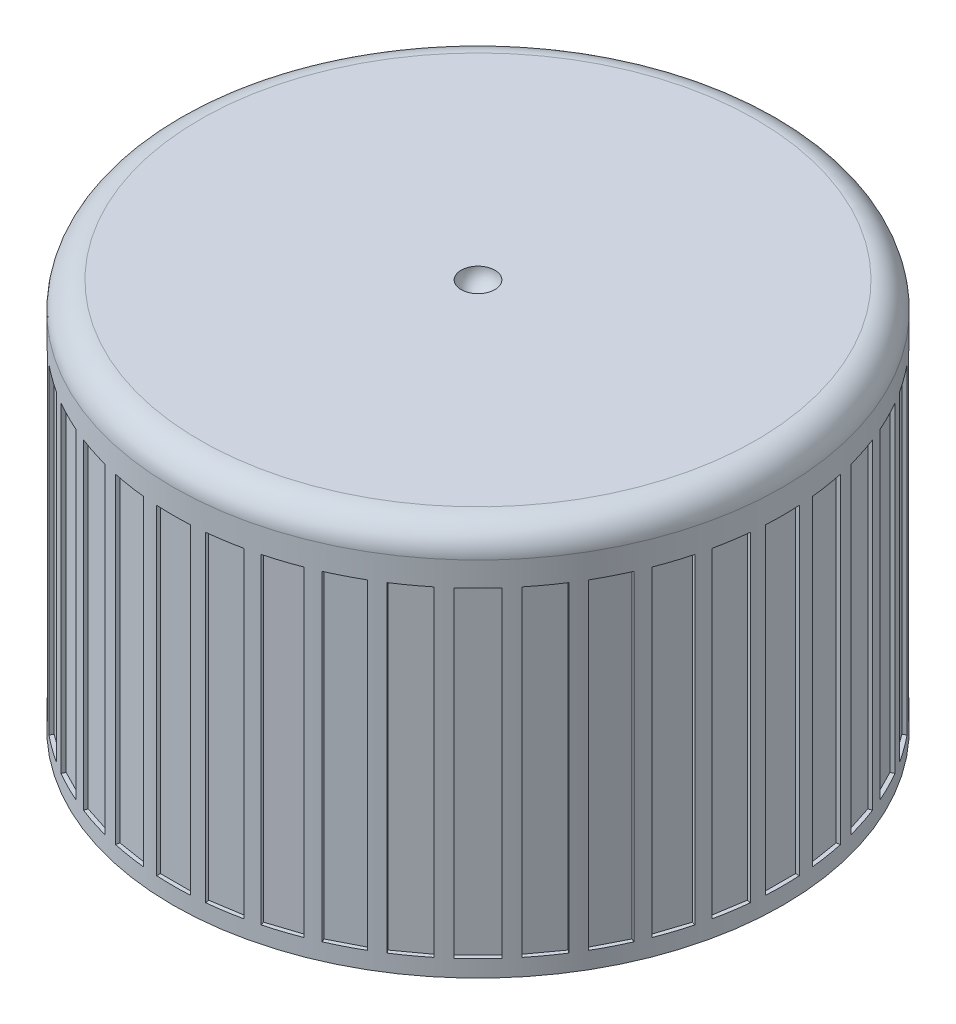
SolidWorks part; units mm, degrees
ref_plane "Front Plane" through (0, 0, 0) normal (0, 0, 1) x (1, 0, 0)
ref_plane "Top Plane" through (0, 0, 0) normal (0, 1, 0) x (1, 0, 0)
ref_plane "Right Plane" through (0, 0, 0) normal (1, 0, 0) x (0, 0, -1)
sketch "Sketch1" plane through (0, 0, 0) normal (0, 0, 1) x (1, 0, 0)
  line L0 (0, 0) -> (9.03, 0) construction
  line L1 (0, 0) -> (0, 7.53) construction
  line L2 (8.23, 11.52) -> (0.5, 11.52)
  line L3 (9.03, 10.72) -> (9.03, 0)
  line L4 (0, 11.02) -> (0, 7.53)
  line L5 (5.51, 7.53) -> (4.3, 7.53)
  line L6 (5.51, 7.53) -> (5.51, 10.02)
  line L7 (5.51, 10.02) -> (6.73, 10.02)
  line L9 (8.5692, 0) -> (9.03, 0)
  line L10 (7.53, 2.04) -> (7.53, 9.22)
  line L16 (3.5, 7.53) -> (2, 7.53)
  line L17 (7.53, 1.52) -> (7.53, 2.04) construction
  line L18 (0, 7.23) -> (0, 7.53)
  line L19 (2, 7.53) -> (2, 7.23)
  line L20 (7.53, 1) -> (7.53, 0) construction
  line L21 (3.9, 7.53) -> (4.3, 7.53) construction
  line L22 (7.53, 0) -> (8.5692, 0) construction
  line L23 (3.9, 7.53) -> (3.5, 7.53) construction
  line L24 (0, 11.52) -> (0, 11.02) construction
  line L25 (0, 11.52) -> (0.5, 11.52) construction
  line L26 (2, 7.23) -> (0, 7.23)
  line L28 (7.53, 1) -> (7.9086, 1.3786)
  line L29 (7.9086, 1.6614) -> (7.53, 2.04)
  line L30 (7.53, 2.04) -> (7.53, 1.52) construction
  line L31 (7.53, 1.52) -> (7.53, 1) construction
  arc A1 (3.5, 7.53) -> (4.3, 7.53) centre (3.9, 7.53) cw
  arc A5 (9.03, 10.72) -> (8.23, 11.52) centre (8.23, 10.72) ccw
  arc A6 (7.53, 9.22) -> (6.73, 10.02) centre (6.73, 9.22) ccw
  arc A8 (0.5, 11.52) -> (0, 11.02) centre (0, 11.52) cw
  arc A9 (7.9086, 1.3786) -> (7.9086, 1.6614) centre (7.7672, 1.52) ccw
  arc A10 (8.5692, 0) -> (7.53, 1) centre (8.5692, 1.04) cw
  point P24 (8.05, 1.52)
  point P26 (7.53, 0)
  point P32 (9.03, 11.52)
  point P35 (7.53, 10.02)
  dimension "D2" = 45
  dimension "D6" = 0.4
  dimension "D15" = 1.04
  dimension "D16" = 1.04
  dimension "D19" = 0.8
  dimension "D7" = 3.9
  dimension "D9" = 0.5
  dimension "D14" = 0.2
  dimension "D1" = 1.5
  dimension "D3" = 10.02
  dimension "D4" = 1
  dimension "D5" = 1.5
  dimension "D8" = 2.02
  dimension "D10" = 2
  dimension "D11" = 2.49
  dimension "D12" = 0.3
  dimension "D13" = 45
  dimension "D17" = 0.8
  dimension "7.52" = 7.53
revolve "Revolve1" add sketch "Sketch1" angle 360 about L1
sketch "Sketch2" plane through (0, 0, 0) normal (0, -1, 0) x (1, 0, 0)
  line L0 (0, 0) -> (9.03, 0) construction
  line L1 (8.8736, -0.8992) -> (9.1205, -0.9383)
  line L2 (8.905, 0.5) -> (9.155, 0.5)
  line L3 (8.905, 0.5) -> (8.905, -0.5)
  line L4 (8.905, -0.5) -> (9.155, -0.5)
  line L5 (9.155, 0.5) -> (9.155, -0.5)
  line L6 (8.905, 0.5) -> (9.155, -0.5) construction
  line L7 (8.905, -0.5) -> (9.155, 0.5) construction
  line L8 (8.8736, -0.8992) -> (8.7171, -1.8869)
  line L9 (8.7171, -1.8869) -> (8.9641, -1.926)
  line L10 (8.7171, -1.8869) -> (9.1205, -0.9383) construction
  line L11 (9.1205, -0.9383) -> (8.9641, -1.926)
  line L12 (8.8736, -0.8992) -> (8.9641, -1.926) construction
  line L13 (8.6237, -2.2763) -> (8.8614, -2.3535)
  line L14 (8.6237, -2.2763) -> (8.3146, -3.2273)
  line L15 (8.3146, -3.2273) -> (8.5524, -3.3046)
  line L16 (8.3146, -3.2273) -> (8.8614, -2.3535) construction
  line L17 (8.8614, -2.3535) -> (8.5524, -3.3046)
  line L18 (8.6237, -2.2763) -> (8.5524, -3.3046) construction
  line L19 (8.1614, -3.5973) -> (8.3842, -3.7108)
  line L20 (8.1614, -3.5973) -> (7.7074, -4.4883)
  line L21 (7.7074, -4.4883) -> (7.9302, -4.6018)
  line L22 (7.7074, -4.4883) -> (8.3842, -3.7108) construction
  line L23 (8.3842, -3.7108) -> (7.9302, -4.6018)
  line L24 (8.1614, -3.5973) -> (7.9302, -4.6018) construction
  line L25 (7.4982, -4.8297) -> (7.7004, -4.9767)
  line L26 (7.4982, -4.8297) -> (6.9104, -5.6387)
  line L27 (6.9104, -5.6387) -> (7.1127, -5.7857)
  line L28 (6.9104, -5.6387) -> (7.7004, -4.9767) construction
  line L29 (7.7004, -4.9767) -> (7.1127, -5.7857)
  line L30 (7.4982, -4.8297) -> (7.1127, -5.7857) construction
  line L31 (6.6503, -5.9432) -> (6.8271, -6.12)
  line L32 (6.6503, -5.9432) -> (5.9432, -6.6503)
  line L33 (5.9432, -6.6503) -> (6.12, -6.8271)
  line L34 (5.9432, -6.6503) -> (6.8271, -6.12) construction
  line L35 (6.8271, -6.12) -> (6.12, -6.8271)
  line L36 (6.6503, -5.9432) -> (6.12, -6.8271) construction
  line L37 (5.6387, -6.9104) -> (5.7857, -7.1127)
  line L38 (5.6387, -6.9104) -> (4.8297, -7.4982)
  line L39 (4.8297, -7.4982) -> (4.9767, -7.7004)
  line L40 (4.8297, -7.4982) -> (5.7857, -7.1127) construction
  line L41 (5.7857, -7.1127) -> (4.9767, -7.7004)
  line L42 (5.6387, -6.9104) -> (4.9767, -7.7004) construction
  line L43 (4.4883, -7.7074) -> (4.6018, -7.9302)
  line L44 (4.4883, -7.7074) -> (3.5973, -8.1614)
  line L45 (3.5973, -8.1614) -> (3.7108, -8.3842)
  line L46 (3.5973, -8.1614) -> (4.6018, -7.9302) construction
  line L47 (4.6018, -7.9302) -> (3.7108, -8.3842)
  line L48 (4.4883, -7.7074) -> (3.7108, -8.3842) construction
  line L49 (3.2273, -8.3146) -> (3.3046, -8.5524)
  line L50 (3.2273, -8.3146) -> (2.2763, -8.6237)
  line L51 (2.2763, -8.6237) -> (2.3535, -8.8614)
  line L52 (2.2763, -8.6237) -> (3.3046, -8.5524) construction
  line L53 (3.3046, -8.5524) -> (2.3535, -8.8614)
  line L54 (3.2273, -8.3146) -> (2.3535, -8.8614) construction
  line L55 (1.8869, -8.7171) -> (1.926, -8.9641)
  line L56 (1.8869, -8.7171) -> (0.8992, -8.8736)
  line L57 (0.8992, -8.8736) -> (0.9383, -9.1205)
  line L58 (0.8992, -8.8736) -> (1.926, -8.9641) construction
  line L59 (1.926, -8.9641) -> (0.9383, -9.1205)
  line L60 (1.8869, -8.7171) -> (0.9383, -9.1205) construction
  line L61 (0.5, -8.905) -> (0.5, -9.155)
  line L62 (0.5, -8.905) -> (-0.5, -8.905)
  line L63 (-0.5, -8.905) -> (-0.5, -9.155)
  line L64 (-0.5, -8.905) -> (0.5, -9.155) construction
  line L65 (0.5, -9.155) -> (-0.5, -9.155)
  line L66 (0.5, -8.905) -> (-0.5, -9.155) construction
  line L67 (-0.8992, -8.8736) -> (-0.9383, -9.1205)
  line L68 (-0.8992, -8.8736) -> (-1.8869, -8.7171)
  line L69 (-1.8869, -8.7171) -> (-1.926, -8.9641)
  line L70 (-1.8869, -8.7171) -> (-0.9383, -9.1205) construction
  line L71 (-0.9383, -9.1205) -> (-1.926, -8.9641)
  line L72 (-0.8992, -8.8736) -> (-1.926, -8.9641) construction
  line L73 (-2.2763, -8.6237) -> (-2.3535, -8.8614)
  line L74 (-2.2763, -8.6237) -> (-3.2273, -8.3146)
  line L75 (-3.2273, -8.3146) -> (-3.3046, -8.5524)
  line L76 (-3.2273, -8.3146) -> (-2.3535, -8.8614) construction
  line L77 (-2.3535, -8.8614) -> (-3.3046, -8.5524)
  line L78 (-2.2763, -8.6237) -> (-3.3046, -8.5524) construction
  line L79 (-3.5973, -8.1614) -> (-3.7108, -8.3842)
  line L80 (-3.5973, -8.1614) -> (-4.4883, -7.7074)
  line L81 (-4.4883, -7.7074) -> (-4.6018, -7.9302)
  line L82 (-4.4883, -7.7074) -> (-3.7108, -8.3842) construction
  line L83 (-3.7108, -8.3842) -> (-4.6018, -7.9302)
  line L84 (-3.5973, -8.1614) -> (-4.6018, -7.9302) construction
  line L85 (-4.8297, -7.4982) -> (-4.9767, -7.7004)
  line L86 (-4.8297, -7.4982) -> (-5.6387, -6.9104)
  line L87 (-5.6387, -6.9104) -> (-5.7857, -7.1127)
  line L88 (-5.6387, -6.9104) -> (-4.9767, -7.7004) construction
  line L89 (-4.9767, -7.7004) -> (-5.7857, -7.1127)
  line L90 (-4.8297, -7.4982) -> (-5.7857, -7.1127) construction
  line L91 (-5.9432, -6.6503) -> (-6.12, -6.8271)
  line L92 (-5.9432, -6.6503) -> (-6.6503, -5.9432)
  line L93 (-6.6503, -5.9432) -> (-6.8271, -6.12)
  line L94 (-6.6503, -5.9432) -> (-6.12, -6.8271) construction
  line L95 (-6.12, -6.8271) -> (-6.8271, -6.12)
  line L96 (-5.9432, -6.6503) -> (-6.8271, -6.12) construction
  line L97 (-6.9104, -5.6387) -> (-7.1127, -5.7857)
  line L98 (-6.9104, -5.6387) -> (-7.4982, -4.8297)
  line L99 (-7.4982, -4.8297) -> (-7.7004, -4.9767)
  line L100 (-7.4982, -4.8297) -> (-7.1127, -5.7857) construction
  line L101 (-7.1127, -5.7857) -> (-7.7004, -4.9767)
  line L102 (-6.9104, -5.6387) -> (-7.7004, -4.9767) construction
  line L103 (-7.7074, -4.4883) -> (-7.9302, -4.6018)
  line L104 (-7.7074, -4.4883) -> (-8.1614, -3.5973)
  line L105 (-8.1614, -3.5973) -> (-8.3842, -3.7108)
  line L106 (-8.1614, -3.5973) -> (-7.9302, -4.6018) construction
  line L107 (-7.9302, -4.6018) -> (-8.3842, -3.7108)
  line L108 (-7.7074, -4.4883) -> (-8.3842, -3.7108) construction
  line L109 (-8.3146, -3.2273) -> (-8.5524, -3.3046)
  line L110 (-8.3146, -3.2273) -> (-8.6237, -2.2763)
  line L111 (-8.6237, -2.2763) -> (-8.8614, -2.3535)
  line L112 (-8.6237, -2.2763) -> (-8.5524, -3.3046) construction
  line L113 (-8.5524, -3.3046) -> (-8.8614, -2.3535)
  line L114 (-8.3146, -3.2273) -> (-8.8614, -2.3535) construction
  line L115 (-8.7171, -1.8869) -> (-8.9641, -1.926)
  line L116 (-8.7171, -1.8869) -> (-8.8736, -0.8992)
  line L117 (-8.8736, -0.8992) -> (-9.1205, -0.9383)
  line L118 (-8.8736, -0.8992) -> (-8.9641, -1.926) construction
  line L119 (-8.9641, -1.926) -> (-9.1205, -0.9383)
  line L120 (-8.7171, -1.8869) -> (-9.1205, -0.9383) construction
  line L121 (-8.905, -0.5) -> (-9.155, -0.5)
  line L122 (-8.905, -0.5) -> (-8.905, 0.5)
  line L123 (-8.905, 0.5) -> (-9.155, 0.5)
  line L124 (-8.905, 0.5) -> (-9.155, -0.5) construction
  line L125 (-9.155, -0.5) -> (-9.155, 0.5)
  line L126 (-8.905, -0.5) -> (-9.155, 0.5) construction
  line L127 (-8.8736, 0.8992) -> (-9.1205, 0.9383)
  line L128 (-8.8736, 0.8992) -> (-8.7171, 1.8869)
  line L129 (-8.7171, 1.8869) -> (-8.9641, 1.926)
  line L130 (-8.7171, 1.8869) -> (-9.1205, 0.9383) construction
  line L131 (-9.1205, 0.9383) -> (-8.9641, 1.926)
  line L132 (-8.8736, 0.8992) -> (-8.9641, 1.926) construction
  line L133 (-8.6237, 2.2763) -> (-8.8614, 2.3535)
  line L134 (-8.6237, 2.2763) -> (-8.3146, 3.2273)
  line L135 (-8.3146, 3.2273) -> (-8.5524, 3.3046)
  line L136 (-8.3146, 3.2273) -> (-8.8614, 2.3535) construction
  line L137 (-8.8614, 2.3535) -> (-8.5524, 3.3046)
  line L138 (-8.6237, 2.2763) -> (-8.5524, 3.3046) construction
  line L139 (-8.1614, 3.5973) -> (-8.3842, 3.7108)
  line L140 (-8.1614, 3.5973) -> (-7.7074, 4.4883)
  line L141 (-7.7074, 4.4883) -> (-7.9302, 4.6018)
  line L142 (-7.7074, 4.4883) -> (-8.3842, 3.7108) construction
  line L143 (-8.3842, 3.7108) -> (-7.9302, 4.6018)
  line L144 (-8.1614, 3.5973) -> (-7.9302, 4.6018) construction
  line L145 (-7.4982, 4.8297) -> (-7.7004, 4.9767)
  line L146 (-7.4982, 4.8297) -> (-6.9104, 5.6387)
  line L147 (-6.9104, 5.6387) -> (-7.1127, 5.7857)
  line L148 (-6.9104, 5.6387) -> (-7.7004, 4.9767) construction
  line L149 (-7.7004, 4.9767) -> (-7.1127, 5.7857)
  line L150 (-7.4982, 4.8297) -> (-7.1127, 5.7857) construction
  line L151 (-6.6503, 5.9432) -> (-6.8271, 6.12)
  line L152 (-6.6503, 5.9432) -> (-5.9432, 6.6503)
  line L153 (-5.9432, 6.6503) -> (-6.12, 6.8271)
  line L154 (-5.9432, 6.6503) -> (-6.8271, 6.12) construction
  line L155 (-6.8271, 6.12) -> (-6.12, 6.8271)
  line L156 (-6.6503, 5.9432) -> (-6.12, 6.8271) construction
  line L157 (-5.6387, 6.9104) -> (-5.7857, 7.1127)
  line L158 (-5.6387, 6.9104) -> (-4.8297, 7.4982)
  line L159 (-4.8297, 7.4982) -> (-4.9767, 7.7004)
  line L160 (-4.8297, 7.4982) -> (-5.7857, 7.1127) construction
  line L161 (-5.7857, 7.1127) -> (-4.9767, 7.7004)
  line L162 (-5.6387, 6.9104) -> (-4.9767, 7.7004) construction
  line L163 (-4.4883, 7.7074) -> (-4.6018, 7.9302)
  line L164 (-4.4883, 7.7074) -> (-3.5973, 8.1614)
  line L165 (-3.5973, 8.1614) -> (-3.7108, 8.3842)
  line L166 (-3.5973, 8.1614) -> (-4.6018, 7.9302) construction
  line L167 (-4.6018, 7.9302) -> (-3.7108, 8.3842)
  line L168 (-4.4883, 7.7074) -> (-3.7108, 8.3842) construction
  line L169 (-3.2273, 8.3146) -> (-3.3046, 8.5524)
  line L170 (-3.2273, 8.3146) -> (-2.2763, 8.6237)
  line L171 (-2.2763, 8.6237) -> (-2.3535, 8.8614)
  line L172 (-2.2763, 8.6237) -> (-3.3046, 8.5524) construction
  line L173 (-3.3046, 8.5524) -> (-2.3535, 8.8614)
  line L174 (-3.2273, 8.3146) -> (-2.3535, 8.8614) construction
  line L175 (-1.8869, 8.7171) -> (-1.926, 8.9641)
  line L176 (-1.8869, 8.7171) -> (-0.8992, 8.8736)
  line L177 (-0.8992, 8.8736) -> (-0.9383, 9.1205)
  line L178 (-0.8992, 8.8736) -> (-1.926, 8.9641) construction
  line L179 (-1.926, 8.9641) -> (-0.9383, 9.1205)
  line L180 (-1.8869, 8.7171) -> (-0.9383, 9.1205) construction
  line L181 (-0.5, 8.905) -> (-0.5, 9.155)
  line L182 (-0.5, 8.905) -> (0.5, 8.905)
  line L183 (0.5, 8.905) -> (0.5, 9.155)
  line L184 (0.5, 8.905) -> (-0.5, 9.155) construction
  line L185 (-0.5, 9.155) -> (0.5, 9.155)
  line L186 (-0.5, 8.905) -> (0.5, 9.155) construction
  line L187 (0.8992, 8.8736) -> (0.9383, 9.1205)
  line L188 (0.8992, 8.8736) -> (1.8869, 8.7171)
  line L189 (1.8869, 8.7171) -> (1.926, 8.9641)
  line L190 (1.8869, 8.7171) -> (0.9383, 9.1205) construction
  line L191 (0.9383, 9.1205) -> (1.926, 8.9641)
  line L192 (0.8992, 8.8736) -> (1.926, 8.9641) construction
  line L193 (2.2763, 8.6237) -> (2.3535, 8.8614)
  line L194 (2.2763, 8.6237) -> (3.2273, 8.3146)
  line L195 (3.2273, 8.3146) -> (3.3046, 8.5524)
  line L196 (3.2273, 8.3146) -> (2.3535, 8.8614) construction
  line L197 (2.3535, 8.8614) -> (3.3046, 8.5524)
  line L198 (2.2763, 8.6237) -> (3.3046, 8.5524) construction
  line L199 (3.5973, 8.1614) -> (3.7108, 8.3842)
  line L200 (3.5973, 8.1614) -> (4.4883, 7.7074)
  line L201 (4.4883, 7.7074) -> (4.6018, 7.9302)
  line L202 (4.4883, 7.7074) -> (3.7108, 8.3842) construction
  line L203 (3.7108, 8.3842) -> (4.6018, 7.9302)
  line L204 (3.5973, 8.1614) -> (4.6018, 7.9302) construction
  line L205 (4.8297, 7.4982) -> (4.9767, 7.7004)
  line L206 (4.8297, 7.4982) -> (5.6387, 6.9104)
  line L207 (5.6387, 6.9104) -> (5.7857, 7.1127)
  line L208 (5.6387, 6.9104) -> (4.9767, 7.7004) construction
  line L209 (4.9767, 7.7004) -> (5.7857, 7.1127)
  line L210 (4.8297, 7.4982) -> (5.7857, 7.1127) construction
  line L211 (5.9432, 6.6503) -> (6.12, 6.8271)
  line L212 (5.9432, 6.6503) -> (6.6503, 5.9432)
  line L213 (6.6503, 5.9432) -> (6.8271, 6.12)
  line L214 (6.6503, 5.9432) -> (6.12, 6.8271) construction
  line L215 (6.12, 6.8271) -> (6.8271, 6.12)
  line L216 (5.9432, 6.6503) -> (6.8271, 6.12) construction
  line L217 (6.9104, 5.6387) -> (7.1127, 5.7857)
  line L218 (6.9104, 5.6387) -> (7.4982, 4.8297)
  line L219 (7.4982, 4.8297) -> (7.7004, 4.9767)
  line L220 (7.4982, 4.8297) -> (7.1127, 5.7857) construction
  line L221 (7.1127, 5.7857) -> (7.7004, 4.9767)
  line L222 (6.9104, 5.6387) -> (7.7004, 4.9767) construction
  line L223 (7.7074, 4.4883) -> (7.9302, 4.6018)
  line L224 (7.7074, 4.4883) -> (8.1614, 3.5973)
  line L225 (8.1614, 3.5973) -> (8.3842, 3.7108)
  line L226 (8.1614, 3.5973) -> (7.9302, 4.6018) construction
  line L227 (7.9302, 4.6018) -> (8.3842, 3.7108)
  line L228 (7.7074, 4.4883) -> (8.3842, 3.7108) construction
  line L229 (8.3146, 3.2273) -> (8.5524, 3.3046)
  line L230 (8.3146, 3.2273) -> (8.6237, 2.2763)
  line L231 (8.6237, 2.2763) -> (8.8614, 2.3535)
  line L232 (8.6237, 2.2763) -> (8.5524, 3.3046) construction
  line L233 (8.5524, 3.3046) -> (8.8614, 2.3535)
  line L234 (8.3146, 3.2273) -> (8.8614, 2.3535) construction
  line L235 (8.7171, 1.8869) -> (8.9641, 1.926)
  line L236 (8.7171, 1.8869) -> (8.8736, 0.8992)
  line L237 (8.8736, 0.8992) -> (9.1205, 0.9383)
  line L238 (8.8736, 0.8992) -> (8.9641, 1.926) construction
  line L239 (8.9641, 1.926) -> (9.1205, 0.9383)
  line L240 (8.7171, 1.8869) -> (9.1205, 0.9383) construction
  circle A0 centre (0, 0) radius 9.03 construction
  point P11 (-9.03, 0)
  point P168 (0, 0)
  dimension "D1" = 1
  dimension "D2" = 0.25
  dimension "D4" = 0.5
  dimension "D3" = 40
extrude "Cut-Extrude1" cut sketch "Sketch2" against normal blind 9.5 from offset 0.5 offset against normal yes
fillet "Fillet2" radius 0.8 1 edges at (0, 7.53, -5.51)
